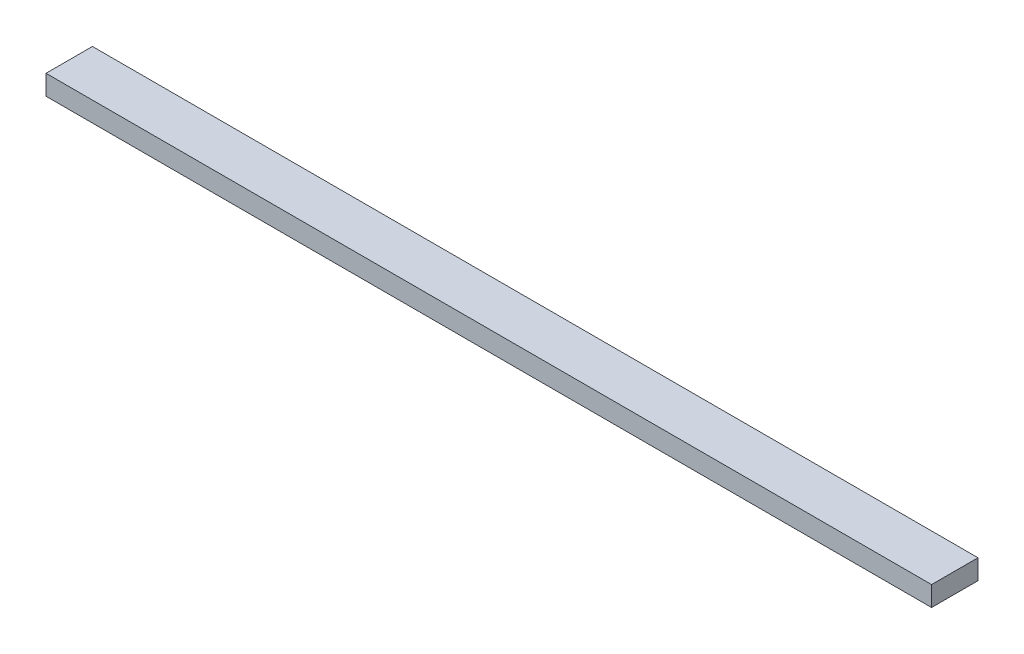
SolidWorks part; units mm, degrees
material "Pine"
ref_plane "Front Plane" through (0, 0, 0) normal (0, 0, 1) x (1, 0, 0)
ref_plane "Top Plane" through (0, 0, 0) normal (0, 1, 0) x (1, 0, 0)
ref_plane "Right Plane" through (0, 0, 0) normal (1, 0, 0) x (0, 0, -1)
sketch "Sketch1" plane through (0, 0, 0) normal (0, 1, 0) x (1, 0, 0)
  line L1 (0, 0) -> (1695.45, 0)
  line L2 (0, 0) -> (0, 88.9)
  line L3 (0, 88.9) -> (1695.45, 88.9)
  line L4 (1695.45, 0) -> (1695.45, 88.9)
  dimension "D1" = 88.9
  dimension "D2" = 1695.45
extrude "Boss-Extrude1" add sketch "Sketch1" along normal blind 38.1
